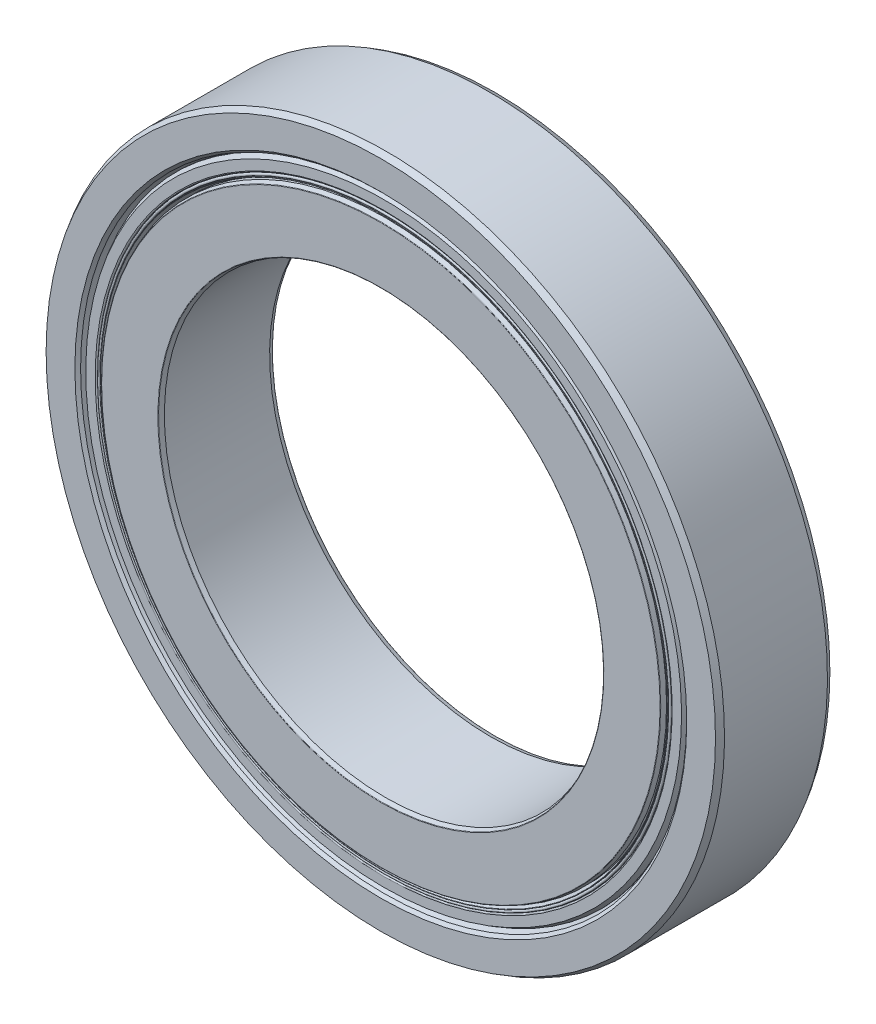
SolidWorks part; units mm, degrees
ref_plane "Front Plane" through (0, 0, 0) normal (0, 0, 1) x (1, 0, 0)
ref_plane "Top Plane" through (0, 0, 0) normal (0, 1, 0) x (1, 0, 0)
ref_plane "Right Plane" through (0, 0, 0) normal (1, 0, 0) x (0, 0, -1)
sketch "Sketch1" plane through (0, 0, 0) normal (0, 0, 1) x (1, 0, 0)
  line L0 (-65, 0) -> (65, 0) construction
  line L1 (-42.5, 0) -> (42.5, 0) construction
  circle A0 centre (0, 0) radius 42.5 construction
  circle A1 centre (0, 0) radius 65 construction
  point P3 (0, 0)
  point P6 (0, 0)
  point P7 (0, -42.5)
  point P11 (0, -65)
  point P12 (0, 42.5)
  point P13 (0, 65)
  dimension "OD" = 130
  dimension "ID" = 85
sketch "Sketch2" plane through (0, 0, 0) normal (1, 0, 0) x (0, 0, -1)
  line L0 (-11, 65) -> (11, 65) construction
  line L1 (0, 65) -> (0, -65) construction
  line L2 (9.9, 65) -> (-9.9, 65)
  line L3 (-9.9, 65) -> (-11, 64.3649)
  line L4 (-11, 64.3649) -> (-11, 58.8344)
  line L5 (-9.2564, 57.85) -> (-5.126, 57.85)
  line L6 (9.2564, 57.85) -> (5.126, 57.85)
  line L7 (11, 64.3649) -> (11, 58.8344)
  line L8 (9.9, 65) -> (11, 64.3649)
  line L9 (-5.126, 57.85) -> (-5.126, 65) construction
  line L10 (-5.126, 61.425) -> (0, 61.425) construction
  line L11 (0, 65) -> (0, -65) construction
  line L12 (-11, 0) -> (11, 0) construction
  line L13 (11, 42.5) -> (-11, 42.5) construction
  line L14 (-11, 42.5) -> (-11, -42.5) construction
  line L15 (-11, -42.5) -> (11, -42.5) construction
  line L16 (11, 65) -> (11, -65) construction
  line L20 (-9.2564, 57.85) -> (-10.45, 58.2844)
  line L21 (-10.45, 58.2844) -> (-11, 58.8344)
  line L26 (10.45, 58.2844) -> (11, 58.8344)
  line L27 (9.2564, 57.85) -> (10.45, 58.2844)
  arc A0 (-5.126, 57.85) -> (5.126, 57.85) centre (0, 55.9626) cw
  circle A1 centre (0, 55.9626) radius 5.4624 construction
  point P17 (0, 0)
  point P21 (0, 65)
  point P30 (0, -42.5)
  dimension "Width" = 22
  dimension "D3" = 10.252
  dimension "For Shaft Diameter" = 85
  dimension "For Housing ID" = 130
  dimension "D4" = 115.7
  dimension "D2" = 20
  dimension "D5" = 45
  dimension "D1" = 30
  dimension "D6" = 1.1
  dimension "D7" = 0.55
sketch "Sketch3" plane through (0, 0, 0) normal (1, 0, 0) x (0, 0, -1)
  line L14 (-9.2564, 57.85) -> (-10.45, 58.2844) construction
  line L15 (-10.45, 58.2844) -> (-11, 58.8344) construction
  line L16 (-11, 64.3649) -> (-11, 58.8344) construction
  line L17 (-9.9, 65) -> (-11, 64.3649) construction
  line L18 (9.9, 65) -> (-9.9, 65) construction
  line L19 (9.9, 65) -> (11, 64.3649) construction
  line L20 (11, 64.3649) -> (11, 58.8344) construction
  line L21 (10.45, 58.2844) -> (11, 58.8344) construction
  line L22 (9.2564, 57.85) -> (10.45, 58.2844) construction
  line L23 (9.2564, 57.85) -> (5.126, 57.85) construction
  line L24 (-9.2564, 57.85) -> (-5.126, 57.85) construction
  line L25 (-9.2564, 57.85) -> (-10.45, 58.2844)
  line L26 (-10.45, 58.2844) -> (-11, 58.8344)
  line L27 (-11, 64.3649) -> (-11, 58.8344)
  line L28 (-9.9, 65) -> (-11, 64.3649)
  line L29 (9.9, 65) -> (-9.9, 65)
  line L30 (9.9, 65) -> (11, 64.3649)
  line L31 (11, 64.3649) -> (11, 58.8344)
  line L32 (10.45, 58.2844) -> (11, 58.8344)
  line L33 (9.2564, 57.85) -> (10.45, 58.2844)
  line L34 (9.2564, 57.85) -> (5.126, 57.85)
  line L35 (-9.2564, 57.85) -> (-5.126, 57.85)
  arc A2 (5.126, 57.85) -> (-5.126, 57.85) centre (0, 55.9626) ccw construction
  arc A3 (5.126, 57.85) -> (-5.126, 57.85) centre (0, 55.9626) ccw
revolve "Revolve1" add sketch "Sketch3" angle 360 about L12
sketch "Sketch4" plane through (0, 0, 0) normal (1, 0, 0) x (0, 0, -1)
  line L0 (0, 65) -> (0, -65) construction
  line L1 (0, 65) -> (0, -65) construction
  line L2 (-10.12, 42.5) -> (-10.9276, 42.794)
  line L3 (-11, 42.8973) -> (-11, 53.6778)
  line L4 (10.12, 54.0751) -> (10.9276, 53.7812)
  line L5 (-10.12, 54.0751) -> (-5.126, 54.0751)
  line L6 (-10.12, 42.5) -> (10.12, 42.5)
  line L7 (11, 64.3649) -> (11, 58.8344) construction
  line L8 (10.12, 42.5) -> (10.9276, 42.794)
  line L9 (5.126, 54.0751) -> (5.126, 42.5) construction
  line L10 (11, 42.8973) -> (11, 53.6778)
  line L11 (10.12, 54.0751) -> (5.126, 54.0751)
  line L12 (-10.12, 54.0751) -> (-10.9276, 53.7812)
  line L14 (5.126, 48.2876) -> (11, 48.2876) construction
  circle A0 centre (0, 55.9626) radius 5.4624 construction
  arc A1 (5.126, 54.0751) -> (-5.126, 54.0751) centre (0, 55.9626) cw
  arc A2 (10.9276, 53.7812) -> (11, 53.6778) centre (10.89, 53.6778) cw
  arc A3 (-10.9276, 53.7812) -> (-11, 53.6778) centre (-10.89, 53.6778) ccw
  arc A4 (10.9276, 42.794) -> (11, 42.8973) centre (10.89, 42.8973) ccw
  arc A5 (-10.9276, 42.794) -> (-11, 42.8973) centre (-10.89, 42.8973) cw
  point P14 (11, 42.8203)
  dimension "D2" = 0.11
  dimension "D1" = 20
  dimension "D3" = 0.88
revolve "Revolve2" add sketch "Sketch4" angle 360 about L12
sketch "Sketch5" plane through (0, 0, 0) normal (1, 0, 0) x (0, 0, -1)
  line L0 (-5.4624, 55.9626) -> (5.4624, 55.9626)
  arc A2 (-5.4624, 55.9626) -> (5.4624, 55.9626) centre (0, 55.9626) cw
  arc A3 (5.126, 57.85) -> (-5.126, 57.85) centre (0, 55.9626) ccw construction
revolve "Revolve3" add sketch "Sketch5" angle 360 about L0
pattern_circular "CirPattern1" count 6 over 360 about axis through (0, 0, 0) along (0, 0, 1) of bodies 104
sketch "Sketch6" plane through (0, 0, 0) normal (1, 0, 0) x (0, 0, -1)
  line L1 (-9.4757, 57.85) -> (-5.4624, 57.85)
  line L2 (-10.45, 57.2875) -> (-10.45, 55.4814)
  line L3 (-10.1688, 55.2001) -> (-5.4624, 55.2001)
  line L4 (-5.4624, 57.85) -> (-5.4624, 55.2001)
  line L6 (-9.9, 65) -> (-11, 64.3649) construction
  line L7 (0, 65) -> (0, 42.5) construction
  line L8 (10.1687, 55.2001) -> (5.4624, 55.2001)
  line L9 (5.4624, 57.85) -> (5.4624, 55.2001)
  line L10 (9.4757, 57.85) -> (5.4624, 57.85)
  line L11 (10.45, 57.2875) -> (10.45, 55.4814)
  line L13 (-10.12, 54.0751) -> (-5.126, 54.0751) construction
  line L14 (-10.45, 57.2875) -> (-9.4757, 57.85)
  line L15 (-9.2564, 57.85) -> (-5.126, 57.85) construction
  line L16 (10.45, 57.2875) -> (9.4757, 57.85)
  arc A0 (-10.45, 55.4814) -> (-10.1688, 55.2001) centre (-10.1688, 55.4814) ccw
  circle A1 centre (0, 55.9626) radius 5.4624 construction
  arc A2 (10.45, 55.4814) -> (10.1687, 55.2001) centre (10.1687, 55.4814) cw
  point P10 (-10.45, 64.6825)
  point P26 (-10.45, 55.2001)
  dimension "D3" = 0.2812
  dimension "D1" = 1.125
  dimension "D2" = 0.5625
revolve "Revolve4" add sketch "Sketch6" angle 360 about L12
sketch "Sketch7" plane through (0, 0, 0) normal (1, 0, 0) x (0, 0, -1)
  line L0 (-5.4624, 54.0751) -> (-9.1615, 54.0751)
  line L5 (-9.1615, 54.0751) -> (-10.4138, 54.5309)
  line L6 (-10.395, 54.6376) -> (-10.1688, 54.6376)
  line L7 (0, 50.5001) -> (0, 42.5) construction
  line L8 (0, 65) -> (0, -65) construction
  line L9 (-10.1688, 55.2001) -> (-5.4624, 55.2001)
  line L12 (-5.4624, 55.2001) -> (-5.4624, 54.0751)
  line L13 (-10.12, 54.0751) -> (-5.126, 54.0751) construction
  line L14 (-10.1688, 55.2001) -> (-5.4624, 55.2001) construction
  line L15 (-5.4624, 57.85) -> (-5.4624, 55.2001) construction
  line L16 (5.4624, 55.2001) -> (5.4624, 54.0751)
  line L17 (10.1687, 55.2001) -> (5.4624, 55.2001)
  line L18 (10.395, 54.6376) -> (10.1687, 54.6376)
  line L19 (9.1615, 54.0751) -> (10.4138, 54.5309)
  line L20 (5.4624, 54.0751) -> (9.1615, 54.0751)
  circle A2 centre (0, 55.9626) radius 5.4624 construction
  arc A5 (-10.4138, 54.5309) -> (-10.395, 54.6376) centre (-10.395, 54.5826) cw
  arc A6 (-10.1688, 54.6376) -> (-10.1688, 55.2001) centre (-10.1688, 54.9189) cw
  arc A7 (10.1687, 54.6376) -> (10.1687, 55.2001) centre (10.1687, 54.9189) ccw
  arc A8 (10.4138, 54.5309) -> (10.395, 54.6376) centre (10.395, 54.5826) ccw
  point P14 (-10.45, 54.9189)
  point P27 (-5.4624, 54.6376)
  point P36 (-10.45, 54.5826)
  dimension "D1" = 20
  dimension "D2" = 0.055
revolve "Revolve5" add sketch "Sketch7" angle 360 about L12
equation "\"D3@Sketch2\"=\"Width@Sketch2\" *.466"
equation "\"D4@Sketch2\"=\"OD@Sketch1\"*.89"
equation "\"D1@Sketch6\"=(\"OD@Sketch1\"-\"ID@Sketch1\")*.025"
equation "\"D2@Sketch6\"=\"D1@Sketch6\"*.5"
equation "\"D3@Sketch6\"=\"D1@Sketch6\"*.25"
equation "\"D3@Sketch4\"=\"Width@Sketch2\"*.04"
equation "\"D2@Sketch4\"=\"D3@Sketch4\"*.125"
equation "\"D6@Sketch2\"=\"Width@Sketch2\"*.05"
equation "\"D7@Sketch2\"=\"D6@Sketch2\"*.5"
equation "\"D2@Sketch7\"=\"D6@Sketch2\"*.05"
